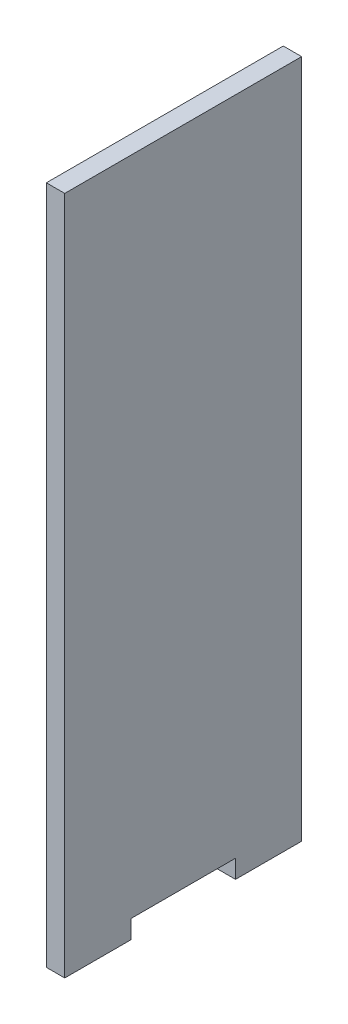
SolidWorks part; units mm, degrees
ref_plane "Front Plane" through (0, 0, 0) normal (0, 0, 1) x (1, 0, 0)
ref_plane "Top Plane" through (0, 0, 0) normal (0, 1, 0) x (1, 0, 0)
ref_plane "Right Plane" through (0, 0, 0) normal (1, 0, 0) x (0, 0, -1)
sketch "Sketch1" plane through (0, 0, 0) normal (1, 0, 0) x (0, 0, -1)
  line L0 (0, 95.1048) -> (0, -34.1162) construction
  line L1 (-32.25, 180) -> (32.25, 180)
  line L2 (-32.25, 180) -> (-32.25, 0)
  line L3 (-14.25, 0) -> (14.25, 0)
  line L4 (32.25, 180) -> (32.25, 0)
  line L5 (-32.25, 0) -> (-32.25, -5)
  line L6 (-32.25, -5) -> (-14.25, -5)
  line L7 (-14.25, -5) -> (-14.25, 0)
  line L8 (14.25, -5) -> (14.25, 0)
  line L9 (32.25, 0) -> (32.25, -5)
  line L10 (32.25, -5) -> (14.25, -5)
  line L11 (-32.25, 0) -> (-14.25, 0) construction
  line L12 (14.25, 0) -> (32.25, 0) construction
  dimension "D1" = 64.5
  dimension "D2" = 180
  dimension "D3" = 5
  dimension "D4" = 18
  dimension "D5" = 28.5
extrude "Boss-Extrude1" add sketch "Sketch1" along normal blind 5
